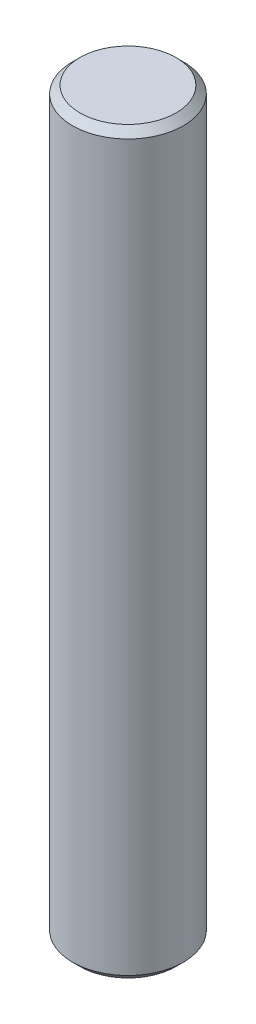
SolidWorks part; units mm, degrees
ref_plane "Plan de face" through (0, 0, 0) normal (0, 0, 1) x (1, 0, 0)
ref_plane "Plan de dessus" through (0, 0, 0) normal (0, 1, 0) x (1, 0, 0)
ref_plane "Plan de droite" through (0, 0, 0) normal (1, 0, 0) x (0, 0, -1)
sketch "Esquisse1" plane through (0, 0, 0) normal (0, 1, 0) x (1, 0, 0)
  circle A0 centre (0, 0) radius 1.5
  dimension "D1" = 3
extrude "Extrusion1" add sketch "Esquisse1" along normal blind 20
chamfer "Chanfrein1" distance 0.2 angle 45 2 edges at (0, 0, 1.5) (0, 20, 1.5)
